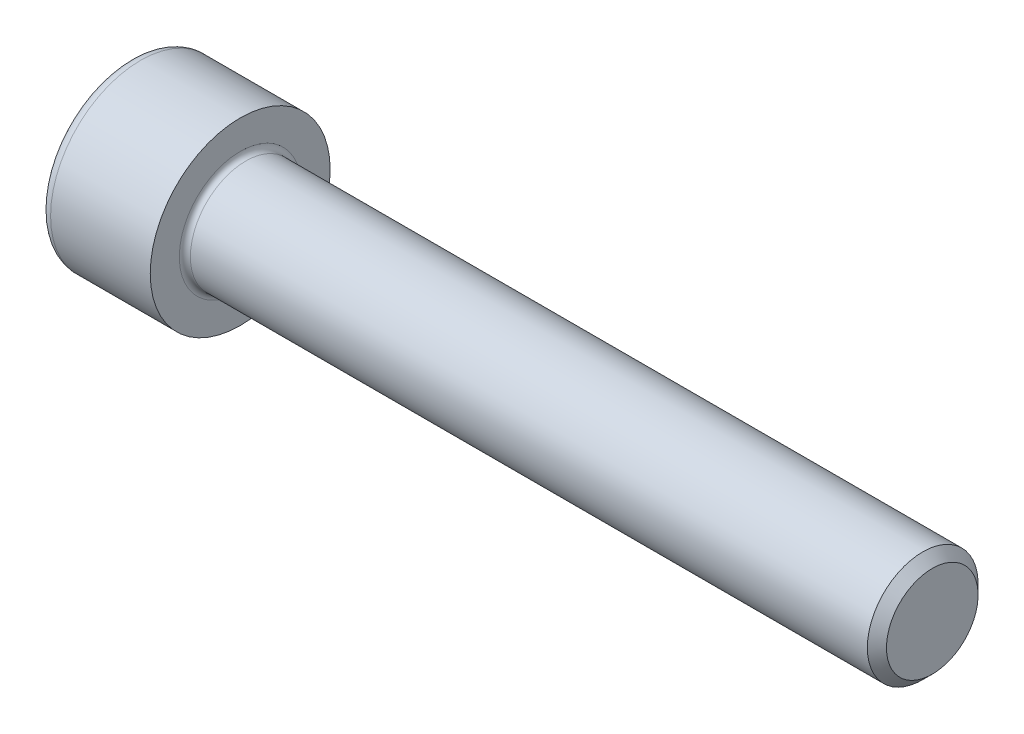
SolidWorks part; units mm, degrees
revolve "Base-Revolve" add sketch "BodySke"
sketch "BodySke" plane through (0, 0, 0) normal (0, 0, 1) x (1, 0, 0)
  line L0 (0, 0) -> (0, 6.5)
  line L1 (0, 6.5) -> (8, 6.5)
  line L2 (8, 6.5) -> (8, 4)
  line L3 (8, 4) -> (57.3095, 4)
  line L4 (58, 3.3095) -> (58, 0)
  line L5 (58, 0) -> (0, 0)
  line L6 (-31.75, 0) -> (127, 0) construction
  line L8 (58, 3.3095) -> (57.3095, 4)
  line L10 (58, -3.3095) -> (57.3095, -4) construction
  line L11 (9.25, 9.525) -> (9.25, 3.175) construction
  line L12 (30, 9.525) -> (30, 3.175) construction
  line L13 (-2, 9.525) -> (-2, 3.175) construction
  dimension "Body_ch_ang" = 45
  dimension "Thread_length" = 60
cosmetic thread "ThreadCosmetic" [suppressed]
fillet "Fillet1" radius 0.4 1 edges at (8, 0, 4)
fillet "Fillet2" radius 0.8 1 edges at (0, 0, 6.5)
ref_plane "Plane1" through (0, 0, 0) normal (0, 0, 1) x (1, 0, 0)
ref_plane "Plane2" through (0, 0, 0) normal (0, 1, 0) x (1, 0, 0)
ref_plane "Plane3" through (0, 0, 0) normal (1, 0, 0) x (0, 0, -1)
sketch "Sketch2" plane through (0, 0, 0) normal (0, 0, 1) x (1, 0, 0)
  line L0 (0, 3.01) -> (4, 3.01)
  line L1 (4, 3.01) -> (5.7378, 0)
  line L2 (-31.75, 0) -> (127, 0) construction
  line L3 (5.7378, 0) -> (0, 0)
  line L4 (0, 0) -> (0, 3.01)
  line L6 (0, 0) -> (47.625, 0) construction
  dimension "D2" = 60
revolve "Hex-PreBroach" cut sketch "Sketch2" angle 360 about L6
sketch "Sketch3" plane through (0, 0, 0) normal (-1, 0, 0) x (0, 0.5, 0.866)
  line L0 (1.7378, 3.01) -> (-1.7378, 3.01)
  line L1 (-1.7378, 3.01) -> (-3.4756, 0)
  line L2 (1.7378, 3.01) -> (3.4756, 0)
  line L3 (1.7378, -3.01) -> (3.4756, 0)
  line L4 (1.7378, -3.01) -> (-1.7378, -3.01)
  line L5 (-1.7378, -3.01) -> (-3.4756, 0)
extrude "Hex" cut sketch "Sketch3" against normal blind 4
sketch "ThdSchSke" plane through (0, 0, 0) normal (0, 0, 1) x (1, 0, 0)
  line L0 (30, -3.3095) -> (29.5165, -4)
  line L1 (30, -3.3095) -> (30.4835, -4)
  line L2 (30.4835, -4) -> (30.4835, -5)
  line L3 (-3.175, 0) -> (5.1513, 0) construction
  line L4 (0, 5.7) -> (0, -5.7) construction
  line L5 (30.4835, -5) -> (29.5165, -5)
  line L6 (29.5165, -5) -> (29.5165, -4)
revolve "ThreadSchematic" [suppressed] cut sketch "ThdSchSke" angle 360 about L3
pattern_linear "ThdSchPat" [suppressed]
equation "\"D2@Sketch3\" = \"Hex_size@Sketch3\" / 2"
equation "\"D1@Sketch3\" = \"Hex_size@Sketch3\" / 2"
equation "\"D1@Sketch2\" = \"Hex_size@Sketch3\" / 2"
equation "\"Thread_minor@ThreadCosmetic\"  =  \"Minor_dia@BodySke\""
equation "\"Depth@Sketch2\" =  \"Key_eng@Hex\""
equation "\"Thread_length@ThreadCosmetic\" = ((sgn( (\"Length@BodySke\" - \"Advance@BodySke\" * 3.0) - \"Thread_nom@BodySke\" )-1)*( (\"Length@BodySke\" - \"Advance@BodySke\" * 3.0) - \"Thread_nom@BodySke\" ))/-2+ \"Thread_nom@BodySke\""
equation "\"Thread_minor@ThdSchSke\" = \"Minor_dia@BodySke\""
equation "\"Diameter@ThdSchSke\" = \"Diameter@BodySke\""
equation "\"Overcut@ThdSchSke\" = \"Diameter@BodySke\" * 1.25"
equation "\"Start@ThdSchSke\" = \"Head_ht@BodySke\" + \"Length@BodySke\" - \"Thread_length@ThreadCosmetic\"  '---Non-countersunk---"
equation "\"Num_threads@ThdSchPat\" = int( \"Thread_length@ThreadCosmetic\" / \"Advance@BodySke\" + 0.999 )  + 1"
equation "\"Advance@ThdSchPat\" = \"Thread_length@ThreadCosmetic\" /  (\"Num_threads@ThdSchPat\" - 1) 'relax it"
equation "\"Num_threads@ThdSchPat\" = \"Num_threads@ThdSchPat\" - sgn( \"Num_threads@ThdSchPat\" - 1) '---chamfered tips only---"
